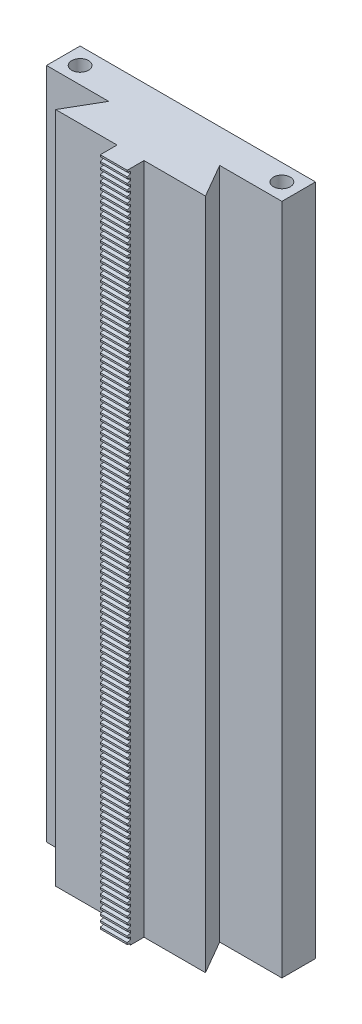
SolidWorks part; units mm, degrees
ref_plane "前视" through (0, 0, 0) normal (0, 0, 1) x (1, 0, 0)
ref_plane "上视" through (0, 0, 0) normal (0, 1, 0) x (1, 0, 0)
ref_plane "右视" through (0, 0, 0) normal (1, 0, 0) x (0, 0, -1)
sketch "草图1" plane through (0, 0, 0) normal (0, 1, 0) x (1, 0, 0)
  line L0 (-22.2735, 0) -> (22.2735, 0)
  line L1 (22.2735, 0) -> (16.5, 10)
  line L2 (16.5, 10) -> (-16.5, 10)
  line L3 (0, 10) -> (0, 0) construction
  line L4 (-22.2735, 0) -> (-16.5, 10)
  dimension "D1" = 60
  dimension "D2" = 16.5
  dimension "D3" = 10
extrude "凸台-拉伸1" add sketch "草图1" along normal blind 200
sketch "草图2" plane through (0, 200, 0) normal (0, 1, 0) x (1, 0, 0)
  line L1 (-22.2735, 0) -> (22.2735, 0) construction
  line L2 (4, -5) -> (-4, -5)
  line L3 (4, -5) -> (4, 5)
  line L4 (4, 5) -> (-4, 5)
  line L5 (-4, -5) -> (-4, 5)
  line L6 (4, -5) -> (-4, 5) construction
  line L7 (4, 5) -> (-4, -5) construction
  point P0 (0, 0)
  dimension "D1" = 10
  dimension "D2" = 8
extrude "凸台-拉伸2" add sketch "草图2" against normal up to surface (200 mm away) up to face at (0, 0, -5)
sketch "草图3" plane through (4, 0, 0) normal (1, 0, 0) x (0, 0, -1)
  line L0 (-5, 199.5) -> (-4, 199.2321)
  line L1 (-5, 200) -> (0, 200) construction
  line L5 (-5, 198.9) -> (-4, 198.9) construction
  line L6 (-5, 0) -> (-5, 200) construction
  line L9 (-5, 198.3) -> (-4, 198.5679)
  line L10 (-5, 199.5) -> (-5, 198.3)
  line L11 (-4, 199.2321) -> (-4, 198.5679)
  dimension "D1" = 0.5
  dimension "D2" = 1
  dimension "D3" = 75
  dimension "D4" = 1.1
extrude "切除-拉伸1" cut sketch "草图3" against normal through all
pattern_linear "阵列(线性)1" count 200 spacing 1.7 along (0, -1, 0) of "切除-拉伸1"
sketch "草图4" plane through (0, 200, 0) normal (0, 1, 0) x (1, 0, 0)
  line L0 (16.5, 10) -> (-16.5, 10) construction
  line L1 (-35, 20) -> (35, 20)
  line L2 (-35, 20) -> (-35, 10)
  line L3 (-35, 10) -> (35, 10)
  line L4 (35, 20) -> (35, 10)
  line L5 (-35, 20) -> (35, 10) construction
  line L6 (-35, 10) -> (35, 20) construction
  point P0 (0, 15)
  dimension "D1" = 10
  dimension "D2" = 70
extrude "凸台-拉伸3" add sketch "草图4" against normal up to surface (200 mm away)
sketch "草图5" plane through (0, 0, -20) normal (0, 0, -1) x (-1, 0, 0)
  line L1 (0, 0) -> (0, 72.4793) construction
  line L2 (-35, 200) -> (35, 200) construction
  line L3 (35, 0) -> (35, 200) construction
  circle A0 centre (31, 130) radius 2
  circle A1 centre (-31, 130) radius 2
  dimension "D1" = 70
  dimension "D2" = 4
  dimension "D3" = 4
extrude "切除-拉伸2" cut sketch "草图5" against normal blind 5
sketch "草图6" plane through (0, 200, 0) normal (0, 1, 0) x (1, 0, 0)
  line L0 (35, 10) -> (35, 20) construction
  line L1 (35, 20) -> (-35, 20) construction
  line L2 (-35, 20) -> (-35, 10) construction
  circle A0 centre (30, 15) radius 2.5
  circle A1 centre (-30, 15) radius 2.5
  dimension "D1" = 5
  dimension "D2" = 5
  dimension "D3" = 5
  dimension "D4" = 5
  dimension "D5" = 5
extrude "切除-拉伸3" cut sketch "草图6" against normal blind 5
